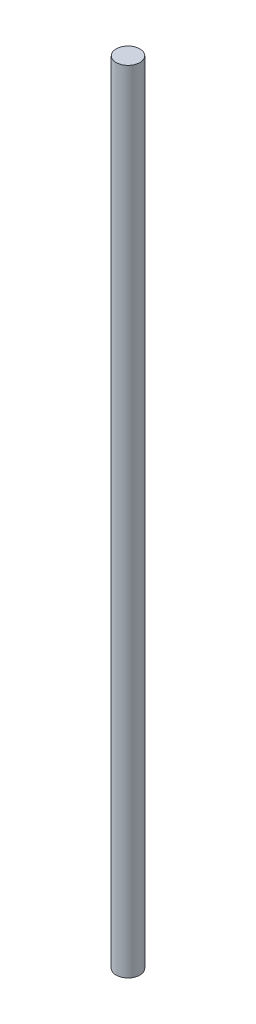
SolidWorks part; units mm, degrees
ref_plane "Front Plane" through (0, 0, 0) normal (0, 0, 1) x (1, 0, 0)
ref_plane "Top Plane" through (0, 0, 0) normal (0, 1, 0) x (1, 0, 0)
ref_plane "Right Plane" through (0, 0, 0) normal (1, 0, 0) x (0, 0, -1)
sketch "Sketch1" plane through (0, 0, 0) normal (0, 1, 0) x (1, 0, 0)
  circle A0 centre (0, 0) radius 2.286
  dimension "D1" = 4.572
extrude "Boss-Extrude1" add sketch "Sketch1" along normal blind 152.4
